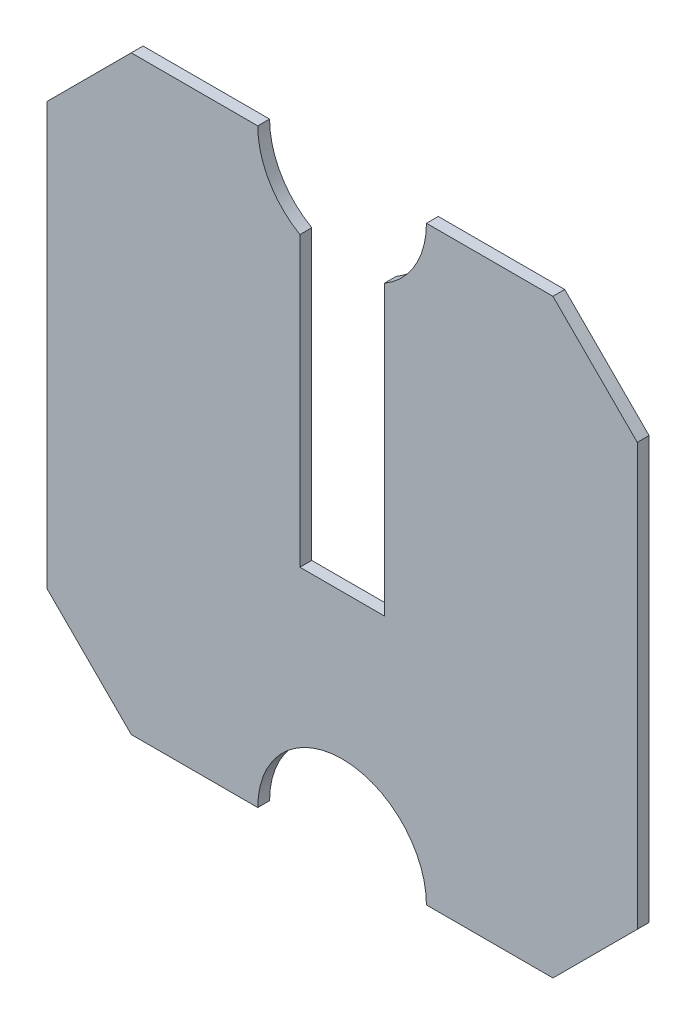
SolidWorks part; units mm, degrees
ref_plane "Front Plane" through (0, 0, 0) normal (0, 0, 1) x (1, 0, 0)
ref_plane "Top Plane" through (0, 0, 0) normal (0, 1, 0) x (1, 0, 0)
ref_plane "Right Plane" through (0, 0, 0) normal (1, 0, 0) x (0, 0, -1)
sketch "Sketch1" plane through (0, 0, 0) normal (0, 0, 1) x (1, 0, 0)
  line L0 (0, 0) -> (0, 250)
  line L1 (0, 250) -> (50, 300)
  line L2 (50, 300) -> (125, 300)
  line L3 (225, 300) -> (300, 300)
  line L4 (300, 300) -> (350, 250)
  line L5 (350, 250) -> (350, 0)
  line L6 (350, 0) -> (300, -50)
  line L7 (300, -50) -> (225, -50)
  line L8 (125, -50) -> (50, -50)
  line L9 (50, -50) -> (0, 0)
  arc A0 (125, 300) -> (225, 300) centre (175, 300) ccw
  arc A1 (225, -50) -> (125, -50) centre (175, -50) ccw
  dimension "D8" = 50
  dimension "D1" = 350
  dimension "D2" = 350
  dimension "D3" = 350
  dimension "D4" = 50
  dimension "D5" = 50
  dimension "D6" = 50
  dimension "D7" = 50
  dimension "D9" = 175
extrude "Boss-Extrude1" add sketch "Sketch1" along normal blind 7
sketch "Sketch2" plane through (0, 0, 7) normal (0, 0, 1) x (1, 0, 0)
  line L0 (175, 250) -> (175, 0) construction
  arc A0 (125, 300) -> (225, 300) centre (175, 300) ccw construction
  arc A1 (225, -50) -> (125, -50) centre (175, -50) ccw construction
sketch "Sketch3" plane through (0, 0, 7) normal (0, 0, 1) x (1, 0, 0)
  line L0 (175, 250) -> (175, 0) construction
  line L1 (200, 298.343) -> (150, 298.343)
  line L2 (200, 298.343) -> (200, 85.8987)
  line L3 (200, 85.8987) -> (150, 85.8987)
  line L4 (150, 298.343) -> (150, 85.8987)
  dimension "D1" = 25
  dimension "D2" = 25
extrude "Cut-Extrude2" cut sketch "Sketch3" against normal through all
